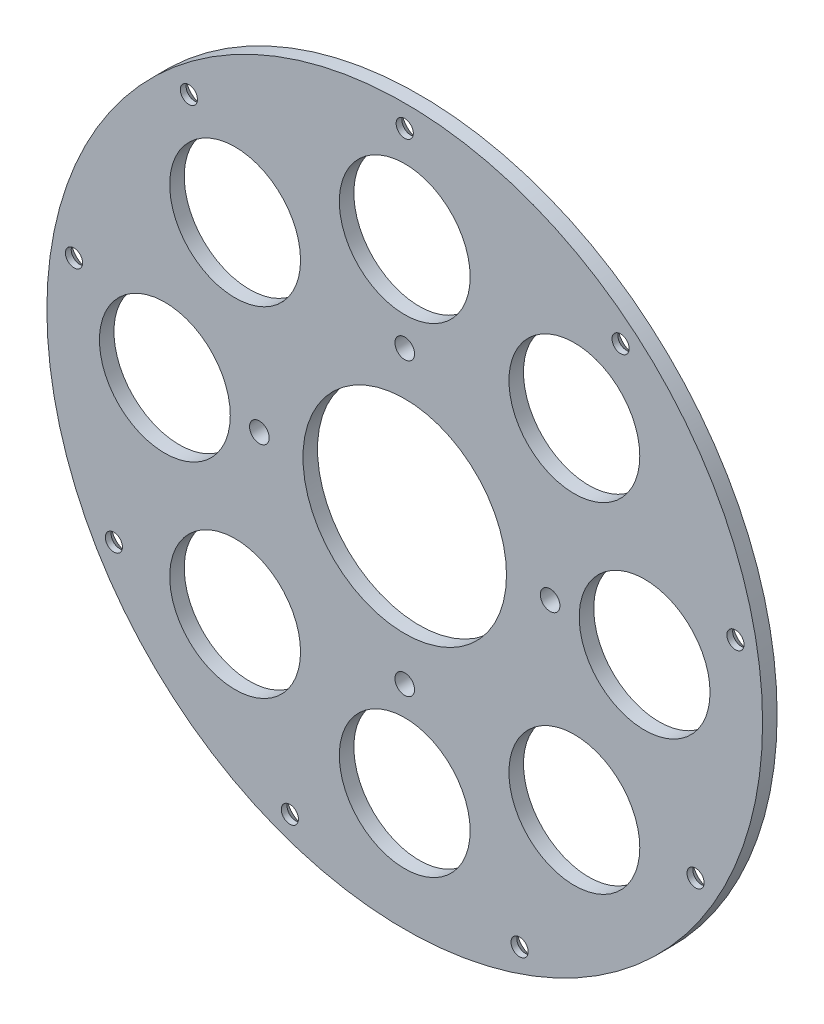
SolidWorks part; units mm, degrees
material "Acier non allié"
ref_plane "Plan de face" through (0, 0, 0) normal (0, 0, 1) x (1, 0, 0)
ref_plane "Plan de dessus" through (0, 0, 0) normal (0, 1, 0) x (1, 0, 0)
ref_plane "Plan de droite" through (0, 0, 0) normal (1, 0, 0) x (0, 0, -1)
sketch "Esquisse1" plane through (0, 0, 0) normal (0, 0, 1) x (1, 0, 0)
  circle A0 centre (0, 0) radius 123.0748
  circle A1 centre (0, 115.5) radius 2.9538
  circle A2 centre (0, 0) radius 35
  circle A4 centre (74.242, 88.4781) radius 2.9538
  circle A5 centre (113.7453, 20.0564) radius 2.9538
  circle A6 centre (100.0259, -57.75) radius 2.9538
  circle A7 centre (39.5033, -108.5345) radius 2.9538
  circle A8 centre (-39.5033, -108.5345) radius 2.9538
  circle A9 centre (-100.0259, -57.75) radius 2.9538
  circle A10 centre (-113.7453, 20.0564) radius 2.9538
  circle A11 centre (-74.242, 88.4781) radius 2.9538
  circle A17 centre (0, 50) radius 3.375
  circle A18 centre (50, 0) radius 3.375
  circle A19 centre (0, -50) radius 3.375
  circle A20 centre (-50, 0) radius 3.375
  circle A21 centre (0, 82.5) radius 22.5
  circle A22 centre (58.3363, 58.3363) radius 22.5
  circle A23 centre (82.5, 0) radius 22.5
  circle A24 centre (58.3363, -58.3363) radius 22.5
  circle A25 centre (0, -82.5) radius 22.5
  circle A26 centre (-58.3363, -58.3363) radius 22.5
  circle A27 centre (-82.5, 0) radius 22.5
  circle A28 centre (-58.3363, 58.3363) radius 22.5
  point P6 (0, 82.5)
  point P7 (0, 82.5)
  point P27 (0, 0)
  point P28 (0, 0)
  point P37 (0, 0)
  point P47 (0, 0)
  point P55 (0, 0)
  dimension "D1" = 115.5
  dimension "D2" = 6.75
  dimension "D5" = 50
  dimension "D7" = 246.1497
  dimension "D8" = 70
  dimension "D9" = 45
  dimension "D4" = 82.5
  dimension "D10" = 8
  dimension "D3" = 9
  dimension "D6" = 4
extrude "Boss.-Extru.1" add sketch "Esquisse1" along normal blind 5
chamfer "Chanfrein1" distance 3 angle 45 9 edges at (77.1958, 88.4781, 0) (2.9538, 115.5, 0) (-71.2882, 88.4781, 0) (-110.7915, 20.0564, 0) (-97.0721, -57.75, 0) (-36.5495, -108.5345, 0) (42.4571, -108.5345, 0) (102.9797, -57.75, 0) (116.6991, 20.0564, 0)
